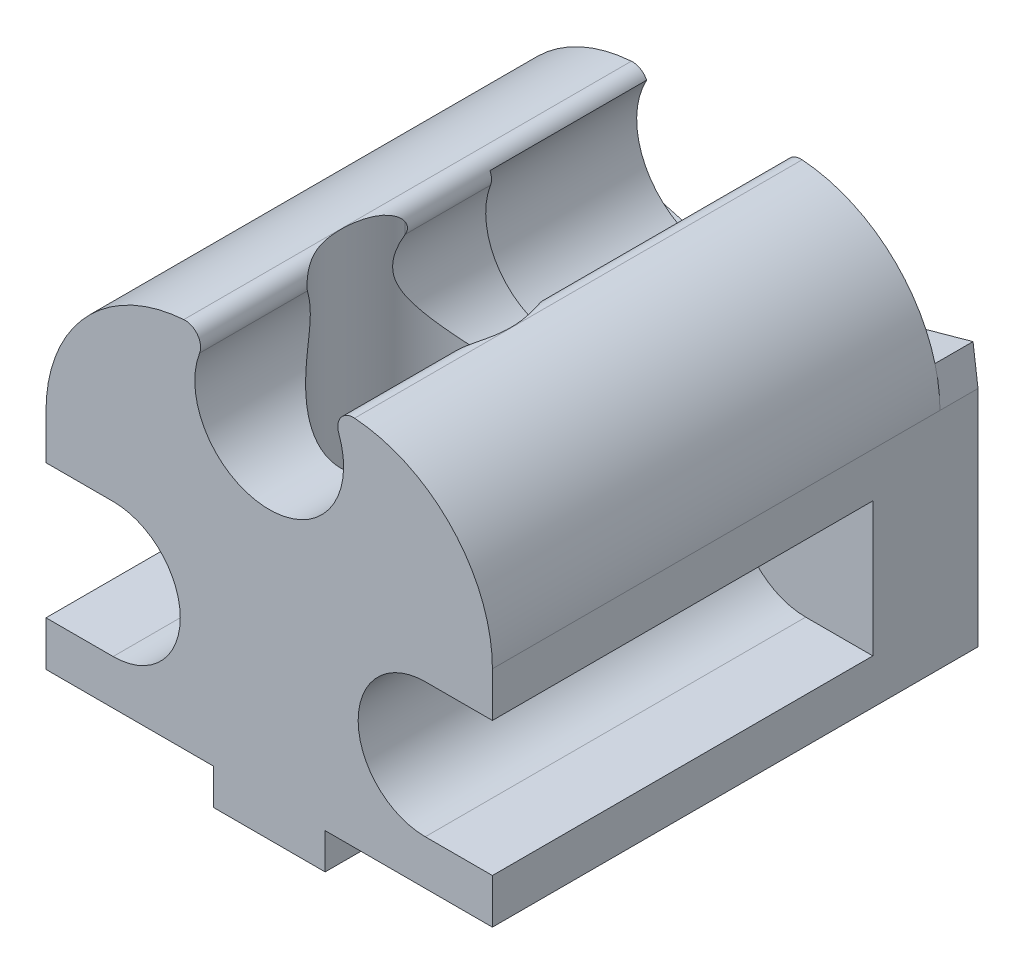
SolidWorks part; units mm, degrees
material "ABS"
ref_plane "Front Plane" through (0, 0, 0) normal (0, 0, 1) x (1, 0, 0)
ref_plane "Top Plane" through (0, 0, 0) normal (0, 1, 0) x (1, 0, 0)
ref_plane "Right Plane" through (0, 0, 0) normal (1, 0, 0) x (0, 0, -1)
sketch "Sketch1" plane through (0, 0, 0) normal (0, 0, 1) x (1, 0, 0)
  line L0 (0, 0) -> (0, 31.5935) construction
  line L1 (-9.975, 0) -> (9.975, 0)
  line L2 (-9.975, 0) -> (-9.975, 10)
  line L4 (9.975, 0) -> (9.975, 10)
  arc A0 (-3.1105, 15.675) -> (3.1105, 15.675) centre (0, 14.5) ccw
  arc A1 (-9.975, 10) -> (-3.8158, 16.6205) centre (-3.3372, 10) cw
  arc A2 (-3.8158, 16.6205) -> (-3.1105, 15.675) centre (-3.7653, 15.9224) cw
  arc A3 (3.8158, 16.6205) -> (3.1105, 15.675) centre (3.7653, 15.9224) ccw
  arc A4 (9.975, 10) -> (3.8158, 16.6205) centre (3.3372, 10) ccw
  point P5 (0, 11.175)
  dimension "D3" = 3.325
  dimension "D4" = 0.7
  dimension "D5" = 4.5
  dimension "D1" = 19.95
  dimension "D2" = 10
  dimension "D6" = 4.5
extrude "Boss-Extrude1" add sketch "Sketch1" along normal blind 20 contours L2 A1 A2 A0 A3 A4 L4 L1
sketch "Sketch2" plane through (0, 0, 20) normal (0, 0, 1) x (1, 0, 0)
  line L0 (-9.975, 0) -> (9.975, 0) construction
  line L1 (-2.5, 0) -> (2.5, 0)
  line L2 (-2.5, 0) -> (-2.5, -1.6)
  line L3 (-2.5, -1.6) -> (2.5, -1.6)
  line L4 (2.5, 0) -> (2.5, -1.6)
  point P6 (0, 0)
  dimension "D1" = 5
  dimension "D2" = 1.6
extrude "Boss-Extrude2" add sketch "Sketch2" against normal blind 13
sketch "Sketch3" plane through (0, 0, 0) normal (0, 0, -1) x (-1, 0, 0)
  circle A0 centre (0, 14.5) radius 3.5786
  arc A1 (-3.1105, 15.675) -> (3.1105, 15.675) centre (0, 14.5) ccw construction
  dimension "D1" = 7.1571
extrude "Cut-Extrude1" cut sketch "Sketch3" against normal blind 7
sketch "Sketch4" plane through (0, 0, 0) normal (0, 0, -1) x (-1, 0, 0)
  line L0 (-9.975, 0) -> (-9.975, 10)
  line L1 (-9.975, 0) -> (-9.975, 10) construction
  line L2 (1.4153, 9.3925) -> (9.7529, 11.7027)
  line L3 (-1.4153, 9.3925) -> (-9.7529, 11.7027)
  line L4 (-9.975, 0) -> (9.975, 0)
  line L5 (9.975, 0) -> (-9.975, 0) construction
  line L6 (9.975, 0) -> (9.975, 10)
  line L7 (-9.975, 10) -> (-9.7529, 11.7027)
  line L8 (9.975, 10) -> (9.7529, 11.7027)
  line L9 (9.975, 0) -> (9.975, 10) construction
  arc A0 (-3.8158, 16.6205) -> (-9.975, 10) centre (-3.3372, 10) ccw construction
  arc A3 (-1.4153, 9.3925) -> (1.4153, 9.3925) centre (0, 14.5) ccw
  arc A4 (9.975, 10) -> (3.8158, 16.6205) centre (3.3372, 10) ccw construction
  arc A5 (-3.1347, 16.2262) -> (3.1347, 16.2262) centre (0, 14.5) ccw construction
  dimension "D1" = 5.3
  dimension "D2" = 2.7973
extrude "Boss-Extrude3" add sketch "Sketch4" along normal blind 1.7
sketch "Sketch6" plane through (0, 0, 0) normal (0, 1, 0) x (1, 0, 0)
  line L0 (0, -20) -> (0, -13) construction
  line L1 (-2.5, -20) -> (2.5, -20) construction
  circle A0 centre (0, -13) radius 2.25
  dimension "D1" = 4.5
  dimension "D2" = 7
extrude "Cut-Extrude2" cut sketch "Sketch6" against normal through all from offset 20
sketch "Sketch7" plane through (0, 0, 0) normal (0, 1, 0) x (1, 0, 0)
  circle A0 centre (0, -13) radius 3.8
  circle A1 centre (0, -13) radius 2.25 construction
  dimension "D1" = 7.6
extrude "Cut-Extrude3" cut sketch "Sketch7" along normal through all from offset 3 contours A0
sketch "Sketch8" plane through (0, 0, -1.7) normal (0, 0, -1) x (-1, 0, 0)
  line L0 (6.975, 5) -> (9.975, 5) construction
  line L1 (9.975, 0) -> (9.975, 10) construction
  circle A0 centre (6.975, 5) radius 1.65
  dimension "D2" = 3.3
  dimension "D1" = 3
extrude "Cut-Extrude4" cut sketch "Sketch8" against normal blind 40
mirror "Mirror1" about plane through (0, 0, 0) normal (1, 0, 0) of "Cut-Extrude4"
sketch "Sketch9" plane through (0, 0, 20) normal (0, 0, 1) x (1, 0, 0)
  line L0 (-9.975, 0) -> (-9.975, 10) construction
  line L1 (-6.975, 8) -> (-9.975, 8)
  line L2 (-9.975, 8) -> (-9.975, 2)
  line L3 (-6.975, 2) -> (-9.975, 2)
  arc A0 (-6.975, 2) -> (-6.975, 8) centre (-6.975, 5) ccw
  circle A1 centre (-6.975, 5) radius 1.65 construction
  dimension "D1" = 3
extrude "Cut-Extrude5" cut sketch "Sketch9" against normal blind 17
sketch "Sketch10" plane through (0, 0, 3) normal (0, 0, 1) x (1, 0, 0)
  circle A0 centre (-6.975, 5) radius 1.65
extrude "Boss-Extrude4" add sketch "Sketch10" against normal blind 0.2
mirror "Mirror2" about plane through (0, 0, 0) normal (1, 0, 0) of "Boss-Extrude4", "Cut-Extrude5"
